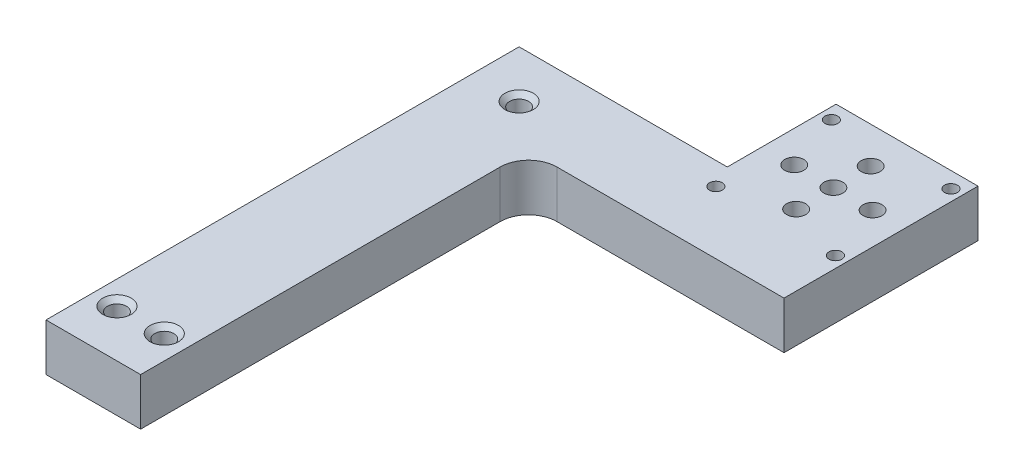
SolidWorks part; units mm, degrees
ref_plane "Front Plane" through (0, 0, 0) normal (0, 0, 1) x (1, 0, 0)
ref_plane "Top Plane" through (0, 0, 0) normal (0, 1, 0) x (1, 0, 0)
ref_plane "Right Plane" through (0, 0, 0) normal (1, 0, 0) x (0, 0, -1)
sketch "Sketch1" plane through (0, 0, 0) normal (0, 1, 0) x (1, 0, 0)
  line L0 (81.28, 40.64) -> (81.28, 92.71)
  line L1 (-12.7, 63.5) -> (12.7, 63.5)
  line L2 (-12.7, 63.5) -> (-12.7, -63.5)
  line L3 (-12.7, -63.5) -> (12.7, -63.5)
  line L4 (12.7, 40.64) -> (12.7, -63.5)
  line L5 (-12.7, 63.5) -> (12.7, -63.5) construction
  line L6 (-12.7, -63.5) -> (12.7, 63.5) construction
  line L7 (12.7, 40.64) -> (81.28, 40.64)
  line L8 (81.28, 92.71) -> (43.18, 92.71)
  line L9 (43.18, 92.71) -> (43.18, 63.5)
  line L10 (12.7, 63.5) -> (43.18, 63.5)
  point P0 (0, 0)
extrude "Boss-Extrude1" add sketch "Sketch1" along normal blind 12.7
sketch "Sketch2" plane through (0, 12.7, 0) normal (0, 1, 0) x (1, 0, 0)
  line L0 (-12.7, -63.5) -> (-6.35, -63.5)
  line L2 (-12.7, -63.5) -> (12.7, -63.5) construction
  line L3 (-6.35, -63.5) -> (-6.35, -50.8)
  line L4 (12.7, -63.5) -> (6.35, -63.5)
  line L5 (6.35, -63.5) -> (6.35, -50.8)
  line L6 (-12.7, 63.5) -> (-12.7, 50.8)
  line L7 (-12.7, 63.5) -> (-12.7, -63.5) construction
  line L8 (-12.7, 50.8) -> (0, 50.8)
  line L9 (0, 50.8) -> (6.35, 50.8)
  line L10 (81.28, 92.71) -> (78.28, 92.71)
  line L11 (81.28, 92.71) -> (43.18, 92.71) construction
  line L12 (78.28, 92.71) -> (78.28, 88.44)
  line L13 (43.18, 92.71) -> (46.18, 92.71)
  line L14 (46.18, 92.71) -> (46.18, 88.44)
  line L15 (62.23, 92.71) -> (62.23, 82.94)
  line L16 (46.18, 92.71) -> (46.18, 57.44)
  line L17 (78.28, 92.71) -> (78.28, 57.44)
  line L18 (43.18, 92.71) -> (43.18, 73.94)
  line L19 (43.18, 92.71) -> (43.18, 63.5) construction
  line L20 (43.18, 73.94) -> (51.68, 73.94)
hole_wizard "1/4-20 Tapped Hole1" positions "Sketch3" profile "Sketch4" tap size "1/4-20" standard "ANSI Inch" end condition up to next
sketch "Sketch3" plane through (0, 12.7, 0) normal (0, 1, 0) x (1, 0, 0)
  point P0 (-6.35, -50.8)
  point P3 (6.35, -50.8)
sketch "Sketch4" plane through (-6.35, 12.7, 50.8) normal (1, 0, 0) x (0, 0, 1)
  line L0 (0, 0) -> (0, 12.7)
  line L1 (0, 12.7) -> (2.5527, 12.7)
  line L2 (2.5527, 12.7) -> (2.5527, 1.2573)
  line L3 (2.5527, 1.2573) -> (3.81, 0)
  line L5 (3.81, 0) -> (0, 0)
  line L6 (-2.5527, 1.2573) -> (-3.81, 0) construction
  line L11 (0, -6.35) -> (0, 107.95) construction
  dimension "Thru Tap Drill Dia." = 5.1054
  dimension "Thru Tap Drill Depth" = 12.7
  dimension "Near C'Sink Dia." = 7.62
  dimension "Near C'Sink Angle" = 90
cosmetic thread "Hole Thread1" parameters "D2"=6.35
cosmetic thread "Hole Thread2" parameters "D2"=6.35
hole_wizard "1/4-20 Tapped Hole2" positions "Sketch9" profile "Sketch10" tap size "1/4-20" standard "ANSI Inch" end condition up to next
sketch "Sketch9" plane through (0, 12.7, 0) normal (0, 1, 0) x (1, 0, 0)
  point P0 (0, 50.8)
sketch "Sketch10" plane through (0, 12.7, -50.8) normal (1, 0, 0) x (0, 0, 1)
  line L0 (0, 0) -> (0, 12.7)
  line L1 (0, 12.7) -> (2.5527, 12.7)
  line L2 (2.5527, 12.7) -> (2.5527, 1.2573)
  line L3 (2.5527, 1.2573) -> (3.81, 0)
  line L5 (3.81, 0) -> (0, 0)
  line L6 (-2.5527, 1.2573) -> (-3.81, 0) construction
  line L11 (0, -6.35) -> (0, 107.95) construction
  dimension "Thru Tap Drill Dia." = 5.1054
  dimension "Thru Tap Drill Depth" = 12.7
  dimension "Near C'Sink Dia." = 7.62
  dimension "Near C'Sink Angle" = 90
cosmetic thread "Hole Thread3" parameters "D2"=6.35
hole_wizard "#29 (0.136) Diameter Hole1" positions "Sketch11" profile "Sketch12" hole size "#29" standard "ANSI Inch" end condition up to next
sketch "Sketch11" plane through (0, 12.7, 0) normal (0, 1, 0) x (1, 0, 0)
  point P0 (46.18, 88.44)
  point P3 (78.28, 88.44)
  point P6 (46.18, 57.44)
  point P9 (78.28, 57.44)
sketch "Sketch12" plane through (46.18, 12.7, -88.44) normal (1, 0, 0) x (0, 0, 1)
  line L0 (0, 0) -> (0, 12.7)
  line L1 (0, 12.7) -> (1.7272, 12.7)
  line L2 (1.7272, 12.7) -> (1.7272, 0)
  line L5 (1.7272, 0) -> (0, 0)
  line L11 (0, -6.35) -> (0, 107.95) construction
  dimension "Thru Hole Dia." = 3.4544
  dimension "Thru Hole Depth" = 12.7
hole_wizard "1/4-20 Tapped Hole4" positions "Sketch15" profile "Sketch16" tap size "1/4-20" standard "ANSI Inch" end condition up to next
sketch "Sketch15" plane through (0, 12.7, 0) normal (0, 1, 0) x (1, 0, 0)
  point P0 (62.23, 82.94)
sketch "Sketch16" plane through (62.23, 12.7, -82.94) normal (1, 0, 0) x (0, 0, 1)
  line L0 (0, 0) -> (0, 12.7)
  line L1 (0, 12.7) -> (2.5527, 12.7)
  line L2 (2.5527, 12.7) -> (2.5527, 0)
  line L5 (2.5527, 0) -> (0, 0)
  line L11 (0, -6.35) -> (0, 107.95) construction
  dimension "Thru Tap Drill Dia." = 5.1054
  dimension "Thru Tap Drill Depth" = 12.7
cosmetic thread "Hole Thread6" parameters "D2"=6.35
pattern_linear "LPattern1" count 3 spacing 10 along (0, 0, 1) of "1/4-20 Tapped Hole4"
hole_wizard "1/4-20 Tapped Hole6" positions "Sketch19" profile "Sketch20" tap size "1/4-20" standard "ANSI Inch" end condition up to next
sketch "Sketch19" plane through (0, 12.7, 0) normal (0, 1, 0) x (1, 0, 0)
  point P0 (51.68, 72.9724)
  point P2 (72.7123, 72.9724)
sketch "Sketch20" plane through (51.68, 12.7, -72.9724) normal (1, 0, 0) x (0, 0, 1)
  line L0 (0, 0) -> (0, 12.7)
  line L1 (0, 12.7) -> (2.5527, 12.7)
  line L2 (2.5527, 12.7) -> (2.5527, 0)
  line L5 (2.5527, 0) -> (0, 0)
  line L11 (0, -6.35) -> (0, 107.95) construction
  dimension "Thru Tap Drill Dia." = 5.1054
  dimension "Thru Tap Drill Depth" = 12.7
cosmetic thread "Hole Thread8" parameters "D2"=6.35
cosmetic thread "Hole Thread9" parameters "D2"=6.35
fillet "Fillet1" radius 7.62 1 edges at (12.7, 6.35, -40.64)
